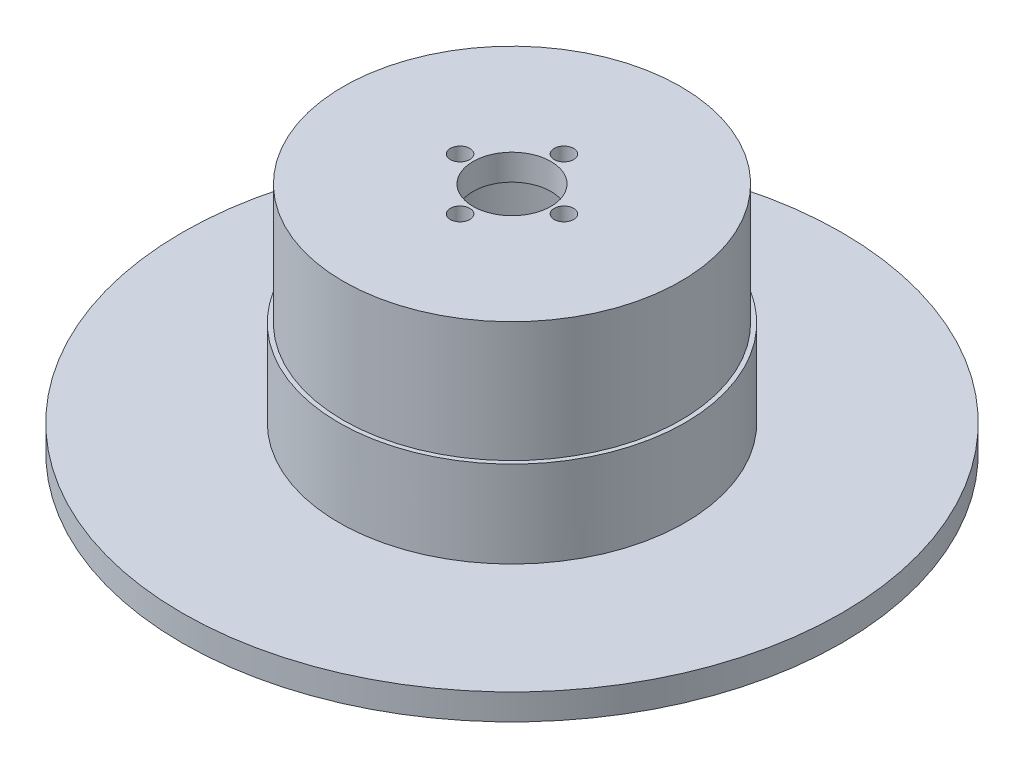
SolidWorks part; units mm, degrees
ref_plane "Front Plane" through (0, 0, 0) normal (0, 0, 1) x (1, 0, 0)
ref_plane "Top Plane" through (0, 0, 0) normal (0, 1, 0) x (1, 0, 0)
ref_plane "Right Plane" through (0, 0, 0) normal (1, 0, 0) x (0, 0, -1)
sketch "Sketch1" plane through (0, 0, 0) normal (0, 1, 0) x (1, 0, 0)
  circle A0 centre (0, 0) radius 14.5
  circle A1 centre (0, 0) radius 19.5
  dimension "D1" = 29
  dimension "D2" = 5
extrude "Boss-Extrude1" add sketch "Sketch1" along normal blind 23.9
sketch "Sketch2" plane through (0, 0, 0) normal (0, -1, 0) x (1, 0, 0)
  circle A0 centre (0, 0) radius 19.5 construction
  circle A1 centre (0, 0) radius 19.5
  circle A2 centre (0, 0) radius 38.1
  dimension "D1" = 76.2
extrude "Boss-Extrude2" add sketch "Sketch2" against normal blind 3
sketch "Sketch3" plane through (0, 3, 0) normal (0, 1, 0) x (1, 0, 0)
  circle A0 centre (0, 0) radius 19.5 construction
  circle A1 centre (0, 0) radius 19.5
  circle A5 centre (0, 0) radius 20
  dimension "D1" = 40
extrude "Boss-Extrude3" add sketch "Sketch3" along normal blind 10
sketch "Sketch4" plane through (0, 23.9, 0) normal (0, 1, 0) x (1, 0, 0)
  circle A0 centre (0, 0) radius 19.5 construction
  circle A1 centre (0, 0) radius 19.5
  circle A2 centre (0, 0) radius 4.5
  circle A3 centre (0, 6) radius 1.125
  circle A4 centre (6, 0) radius 1.125
  circle A5 centre (0, -6) radius 1.125
  circle A6 centre (-6, 0) radius 1.125
  point P15 (0, 0)
  dimension "D1" = 9
  dimension "D2" = 2.25
  dimension "D3" = 6
  dimension "D4" = 4
extrude "Boss-Extrude4" add sketch "Sketch4" along normal blind 3
